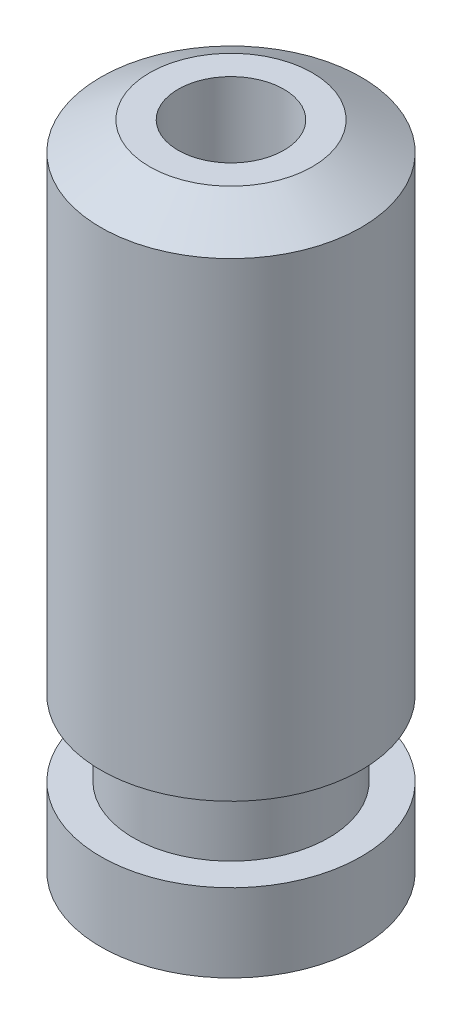
SolidWorks part; units mm, degrees
ref_plane "Front Plane" through (0, 0, 0) normal (0, 0, 1) x (1, 0, 0)
ref_plane "Top Plane" through (0, 0, 0) normal (0, 1, 0) x (1, 0, 0)
ref_plane "Right Plane" through (0, 0, 0) normal (1, 0, 0) x (0, 0, -1)
sketch "Sketch2" plane through (0, 0, 0) normal (0, 0, 1) x (1, 0, 0)
  line L0 (0, 0) -> (8, 0)
  line L1 (8, 0) -> (8, 4.8)
  line L2 (8, 4.8) -> (6, 4.8)
  line L3 (6, 4.8) -> (6, 9.4)
  line L4 (0, 40) -> (5, 40)
  line L5 (0, 40) -> (0, 0)
  line L6 (6, 9.4) -> (8, 9.4)
  line L7 (8, 38.2679) -> (8, 9.4)
  line L8 (5, 40) -> (8, 38.2679)
  dimension "D1" = 8
  dimension "D2" = 6
  dimension "D3" = 4.8
  dimension "D4" = 4.6
  dimension "D5" = 40
  dimension "D6" = 5
  dimension "D7" = 30
revolve "Revolve1" add sketch "Sketch2" angle 360 about L5
sketch "Sketch3" plane through (0, 0, 0) normal (0, -1, 0) x (1, 0, 0)
  circle A0 centre (0, 0) radius 3.25
  dimension "D1" = 6.5
extrude "Cut-Extrude1" cut sketch "Sketch3" against normal through all
